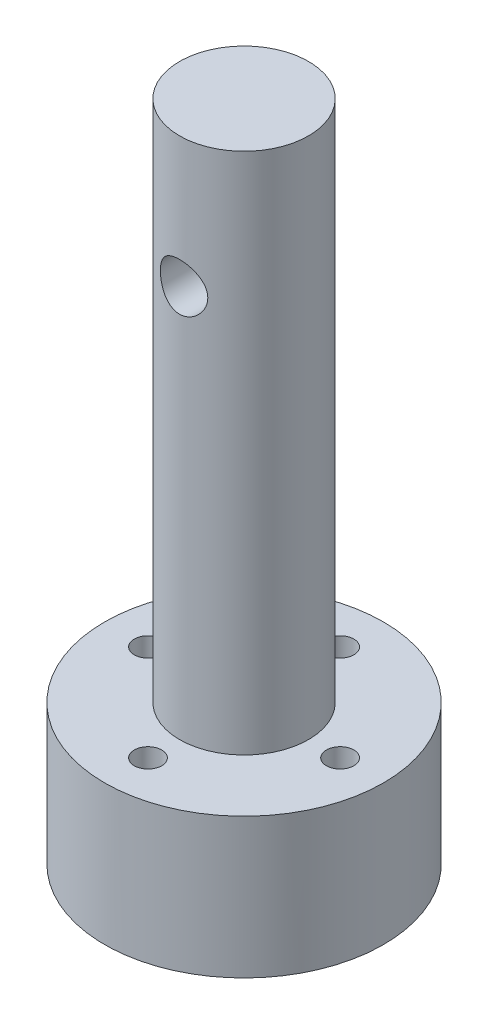
SolidWorks part; units mm, degrees
ref_plane "Front Plane" through (0, 0, 0) normal (0, 0, 1) x (1, 0, 0)
ref_plane "Top Plane" through (0, 0, 0) normal (0, 1, 0) x (1, 0, 0)
ref_plane "Right Plane" through (0, 0, 0) normal (1, 0, 0) x (0, 0, -1)
sketch "Sketch1" plane through (0, 0, 0) normal (0, 1, 0) x (1, 0, 0)
  circle A0 centre (0, 0) radius 10.16
  circle A1 centre (7, 0) radius 1
  circle A2 centre (0, -7) radius 1
  circle A3 centre (-7, 0) radius 1
  circle A4 centre (0, 7) radius 1
  point P14 (0, 0)
  dimension "D1" = 20.32
  dimension "D2" = 2
  dimension "D3" = 7
  dimension "D4" = 4
extrude "Boss-Extrude1" add sketch "Sketch1" along normal blind 19.05
sketch "Sketch2" plane through (0, 19.05, 0) normal (0, 1, 0) x (1, 0, 0)
  circle A0 centre (0, 0) radius 4.699
  dimension "D1" = 9.398
extrude "Boss-Extrude2" add sketch "Sketch2" along normal blind 38.1
sketch "Sketch3" plane through (0, 0, 0) normal (0, 1, 0) x (1, 0, 0)
  circle A0 centre (0, 0) radius 3.429
  dimension "D1" = 6.858
sketch "Sketch4" plane through (0, 0, 0) normal (0, -1, 0) x (1, 0, 0)
  circle A1 centre (0, 0) radius 10.16
  circle A2 centre (0, 0) radius 10.16
  dimension "D1" = 0
extrude "Cut-Extrude2" cut sketch "Sketch4" against normal blind 8.842
extrude "Cut-Extrude3" cut sketch "Sketch3" along normal blind 3.175 from surface at 8.842 starting at face at (7, 8.842, -1)
sketch "Sketch5" plane through (0, 0, 0) normal (0, 0, 1) x (1, 0, 0)
  line L0 (4.699, 57.15) -> (-4.699, 57.15) construction
  circle A0 centre (0, 47.625) radius 1.727
  dimension "D1" = 3.454
  dimension "D2" = 9.525
extrude "Cut-Extrude4" cut sketch "Sketch5" against normal through all both and the other way through all
equation "\"D3@Sketch1\"=7MM"
equation "\"D2@Sketch1\"=2MM"
equation "\"tightTol\"= 0.005in"
equation "\"normTol\"= 0.01in"
equation "\"looseTol\"= 0.02in"
equation "\"D1@Sketch2\"=0.375000-\"tightTol\""
equation "\"D1@Sketch3\"=1/4+\"looseTol\""
equation "\"D1@Cut-Extrude2\"= 15.7mm - 0.25 - \"looseTol\""
equation "\"D1@Sketch5\"=3.2mm+\"normTol\""
